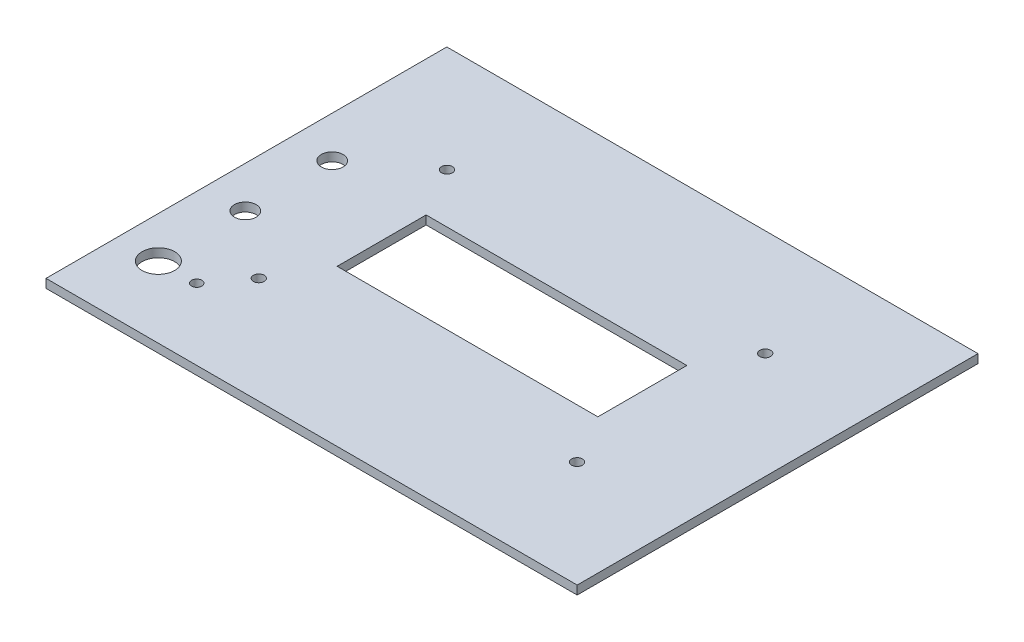
SolidWorks part; units mm, degrees
ref_plane "Front Plane" through (0, 0, 0) normal (0, 0, 1) x (1, 0, 0)
ref_plane "Top Plane" through (0, 0, 0) normal (0, 1, 0) x (1, 0, 0)
ref_plane "Right Plane" through (0, 0, 0) normal (1, 0, 0) x (0, 0, -1)
sketch "Sketch1" plane through (0, 0, 0) normal (0, 1, 0) x (1, 0, 0)
  line L1 (0, 0) -> (155.2448, 0)
  line L2 (0, 0) -> (0, 117.1448)
  line L3 (0, 117.1448) -> (155.2448, 117.1448)
  line L4 (155.2448, 0) -> (155.2448, 117.1448)
  dimension "D1" = 117.1448
  dimension "D2" = 155.2448
extrude "Boss-Extrude1" add sketch "Sketch1" along normal blind 2.54
sketch "Sketch2" plane through (0, 2.54, 0) normal (0, 1, 0) x (1, 0, 0)
  line L1 (39.497, 71.5978) -> (115.697, 71.5978)
  line L2 (39.497, 71.5978) -> (39.497, 45.5978)
  line L3 (39.497, 45.5978) -> (115.697, 45.5978)
  line L4 (115.697, 71.5978) -> (115.697, 45.5978)
  line L5 (155.2448, 117.1448) -> (0, 117.1448) construction
  line L6 (0, 117.1448) -> (0, 0) construction
  circle A0 centre (31.097, 86.0978) radius 1.5875
  circle A1 centre (31.097, 31.0978) radius 1.5875
  circle A2 centre (124.097, 86.0978) radius 1.5875
  circle A3 centre (124.097, 31.0978) radius 1.5875
  circle A4 centre (12.047, 71.5978) radius 3.175
  circle A5 centre (12.047, 46.1978) radius 3.175
  circle A6 centre (12.047, 20.7978) radius 4.7625
  circle A7 centre (23.247, 20.7978) radius 1.5
  dimension "D5" = 3.175
  dimension "D6" = 3.175
  dimension "D7" = 3.175
  dimension "D8" = 3.175
  dimension "D13" = 6.35
  dimension "D14" = 6.35
  dimension "D17" = 9.525
  dimension "D20" = 3
  dimension "D1" = 26
  dimension "D2" = 76.2
  dimension "D3" = 45.547
  dimension "D4" = 39.497
  dimension "D9" = 55
  dimension "D10" = 93
  dimension "D11" = 8.4
  dimension "D12" = 14.5
  dimension "D15" = 19.05
  dimension "D16" = 25.4
  dimension "D18" = 25.4
  dimension "D19" = 11.2
extrude "Cut-Extrude1" cut sketch "Sketch2" against normal blind 2.54
equation "\"D3@Sketch2\"=(4.61-\"D1@Sketch2\")/2"
equation "\"D4@Sketch2\"=(6.11-\"D2@Sketch2\")/2"
equation "\"D11@Sketch2\"=(\"D10@Sketch2\"-\"D2@Sketch2\")/2"
equation "\"D12@Sketch2\"=(\"D9@Sketch2\"-\"D1@Sketch2\")/2"
